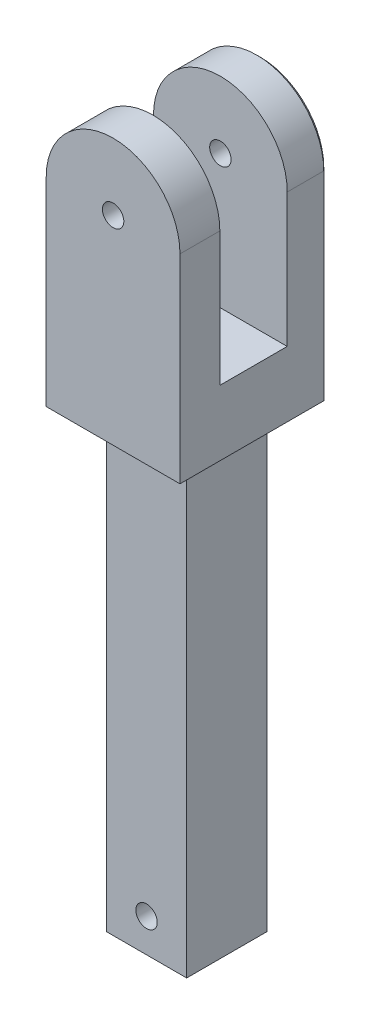
SolidWorks part; units mm, degrees
ref_plane "前基準面" through (0, 0, 0) normal (0, 0, 1) x (1, 0, 0)
ref_plane "上基準面" through (0, 0, 0) normal (0, 1, 0) x (1, 0, 0)
ref_plane "右基準面" through (0, 0, 0) normal (1, 0, 0) x (0, 0, -1)
sketch "草圖1" plane through (0, 0, 0) normal (0, 0, 1) x (1, 0, 0)
  line L0 (0, 0) -> (0, -11.05)
  line L1 (-10, 0) -> (-10, -30.2764)
  line L3 (10, -30.2764) -> (10, 0)
  line L4 (-10, -30.2764) -> (10, -30.2764)
  circle A1 centre (0, 0) radius 1.6
  arc A2 (10, 0) -> (-10, 0) centre (0, 0) ccw
  dimension "D1" = 11.05
  dimension "D2" = 3.2
  dimension "D3" = 20
extrude "填料-伸長1" add sketch "草圖1" along normal blind 12
sketch "草圖2" plane through (10, 0, 0) normal (1, 0, 0) x (0, 0, -1)
  line L0 (-12, 0) -> (-9.1, 0)
  line L1 (-12, 0) -> (0, 0) construction
  line L2 (-12, 10) -> (-12, 0) construction
  line L3 (0, 0) -> (-2.9, 0)
  line L4 (-6, 0) -> (-3, 0)
  line L5 (-6, 0) -> (-9, 0)
  line L6 (-9, 0) -> (-9, 15.7808)
  line L7 (-9, 15.7808) -> (-3, 15.7808)
  line L8 (-3, 15.7808) -> (-3, 0)
  line L9 (-3, 0) -> (-3, -20)
  line L10 (-9, 0) -> (-8.6005, -20)
  line L11 (-8.6005, -20) -> (-3, -20)
  line M8 (0, 0) -> (-12, 0)
  dimension "D1" = 2.9
  dimension "D2" = 2.9
  dimension "D3" = 3
  dimension "D4" = 3
  dimension "D5" = 20
extrude "除料-伸長1" cut sketch "草圖2" against normal through all contours L8 L7 L6 M8 | L10 L11 L9 M8
sketch "草圖11" plane through (10, 0, 0) normal (1, 0, 0) x (0, 0, -1)
  line L0 (-9, 0) -> (-9, -20)
  line L1 (-9, -20) -> (-8.6005, -20)
  line L2 (-9, 0) -> (-8.6005, -20)
extrude "除料-伸長6" cut sketch "草圖11" against normal through all
sketch "草圖12" plane through (0, 0, 12) normal (0, 0, 1) x (1, 0, 0)
  line L0 (-10, 0) -> (-10, -30.2764)
  line L1 (-10, -30.2764) -> (10, -30.2764)
  line L2 (10, -30.2764) -> (10, 0)
  circle A0 centre (0, 0) radius 1.45
  circle A1 centre (0, 0) radius 10
  circle M1 centre (0, 0) radius 1.6
  line M2 (10, -30.2764) -> (10, 0)
  arc M3 (10, 0) -> (-10, 0) centre (0, 0) ccw
  line M4 (-10, 0) -> (-10, -30.2764)
  line M5 (-10, -30.2764) -> (10, -30.2764)
extrude "填料-伸長11" add sketch "草圖12" along normal blind 5 contours A1 M3 M1 | A1 M4 M5 M2
sketch "草圖13" plane through (0, 0, 0) normal (0, 0, -1) x (-1, 0, 0)
  line L0 (-10, 0) -> (-10, -30.2764)
  line L1 (-10, -30.2764) -> (10, -30.2764)
  line L2 (10, 0) -> (10, -30.2764) construction
  line L3 (10, -30.2764) -> (-10, -30.2764) construction
  line L4 (10, -30.2764) -> (10, 0)
  circle A0 centre (0, 0) radius 1.45
  circle A1 centre (0, 0) radius 10
  circle M1 centre (0, 0) radius 1.6
  line M2 (-10, 0) -> (-10, -30.2764)
  line M3 (-10, -30.2764) -> (10, -30.2764)
  line M4 (10, -30.2764) -> (10, 0)
  arc M5 (10, 0) -> (-10, 0) centre (0, 0) ccw
extrude "填料-伸長12" add sketch "草圖13" along normal blind 5 contours A1 M5 M1 | A1 M2 M3 M4
sketch "草圖14" plane through (-10, 0, 0) normal (-1, 0, 0) x (0, 0, 1)
  line L0 (3, -20) -> (0.96, -20)
  line L1 (0.96, -20) -> (0.96, 10)
  line L2 (3, 10) -> (-5, 10) construction
  line L3 (0.96, 10) -> (3, 10)
  line L5 (3, 10) -> (11.04, 10)
  line L6 (9, -20) -> (11.04, -20)
  line L7 (11.04, -20) -> (11.04, 10)
  line L8 (17, 10) -> (9, 10) construction
  line L9 (0.96, 10) -> (11.04, 10)
  line L10 (11.04, -20) -> (0.96, -20)
  line L11 (0.96, 10) -> (0.96, -20)
  line L12 (0.96, 10) -> (11.04, 10)
  line M7 (9, 0) -> (9, -20)
  line M8 (9, -20) -> (3, -20)
  line M9 (3, -20) -> (3, 0)
  line M10 (3, 0) -> (-5, 0)
  line M14 (17, 0) -> (9, 0)
  dimension "D1" = 2.04
  dimension "D2" = 2.04
extrude "除料-伸長7" cut sketch "草圖14" against normal through all contours L7 L5 L3 L1 M14 M10 M9 M8 M7 | L1 L0 M9 M10 | L6 L7 M14 M7
sketch "草圖15" plane through (0, -30.2764, 0) normal (0, -1, 0) x (1, 0, 0)
  line L0 (-10, 6) -> (10, 6)
  line L1 (-10, 17) -> (-10, -5) construction
  line L2 (10, 17) -> (10, -5) construction
  line L3 (0, 17) -> (0, -5)
  line L4 (-10, 17) -> (10, 17) construction
  line L5 (10, -5) -> (-10, -5) construction
  line L7 (-6, 0) -> (6, 0)
  line L8 (-6, 0) -> (-6, 12)
  line L9 (-6, 12) -> (6, 12)
  line L10 (6, 0) -> (6, 12)
  line L11 (-6, 0) -> (6, 12) construction
  line L12 (-6, 12) -> (6, 0) construction
  point P12 (0, 6)
  dimension "D1" = 12
  dimension "D2" = 12
extrude "填料-伸長13" add sketch "草圖15" along normal blind 68 contours L0 L10 L9 L3 | L9 L8 L0 L3 | L7 L10 L0 L3 | L8 L7 L3 L0
sketch "草圖17" plane through (0, 0, 0) normal (0, 0, -1) x (-1, 0, 0)
  line L0 (0, -98.2764) -> (0, -93.2764)
  line L1 (6, -98.2764) -> (-6, -98.2764) construction
  circle A0 centre (0, -93.2764) radius 1.6
  dimension "D2" = 3.2
  dimension "D1" = 5
extrude "除料-伸長8" cut sketch "草圖17" against normal through all
chamfer "導角1" distance 0.5 angle 45 7 edges at (10, -15.1382, -5) (-10, -15.1382, -5) (0, -30.2764, 17) (0, 10, -5) (0, -30.2764, -5) (-10, -30.2764, 6) (10, -30.2764, 6)
